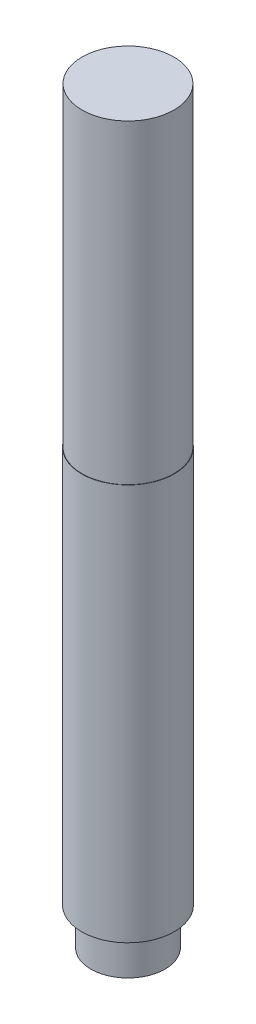
SolidWorks part; units mm, degrees
ref_plane "Front Plane" through (0, 0, 0) normal (0, 0, 1) x (1, 0, 0)
ref_plane "Top Plane" through (0, 0, 0) normal (0, 1, 0) x (1, 0, 0)
ref_plane "Right Plane" through (0, 0, 0) normal (1, 0, 0) x (0, 0, -1)
sketch "Sketch1" plane through (0, 0, 0) normal (0, 1, 0) x (1, 0, 0)
  circle A0 centre (0, 0) radius 12.5
extrude "Boss-Extrude1" add sketch "Sketch1" along normal blind 107
sketch "Sketch2" plane through (0, 107, 0) normal (0, 1, 0) x (1, 0, 0)
  circle A0 centre (0, 0) radius 12.4
extrude "Boss-Extrude2" add sketch "Sketch2" along normal blind 85
sketch "Sketch3" plane through (0, 0, 0) normal (0, -1, 0) x (1, 0, 0)
  circle A0 centre (0, 0) radius 10
extrude "Boss-Extrude3" add sketch "Sketch3" along normal blind 10
